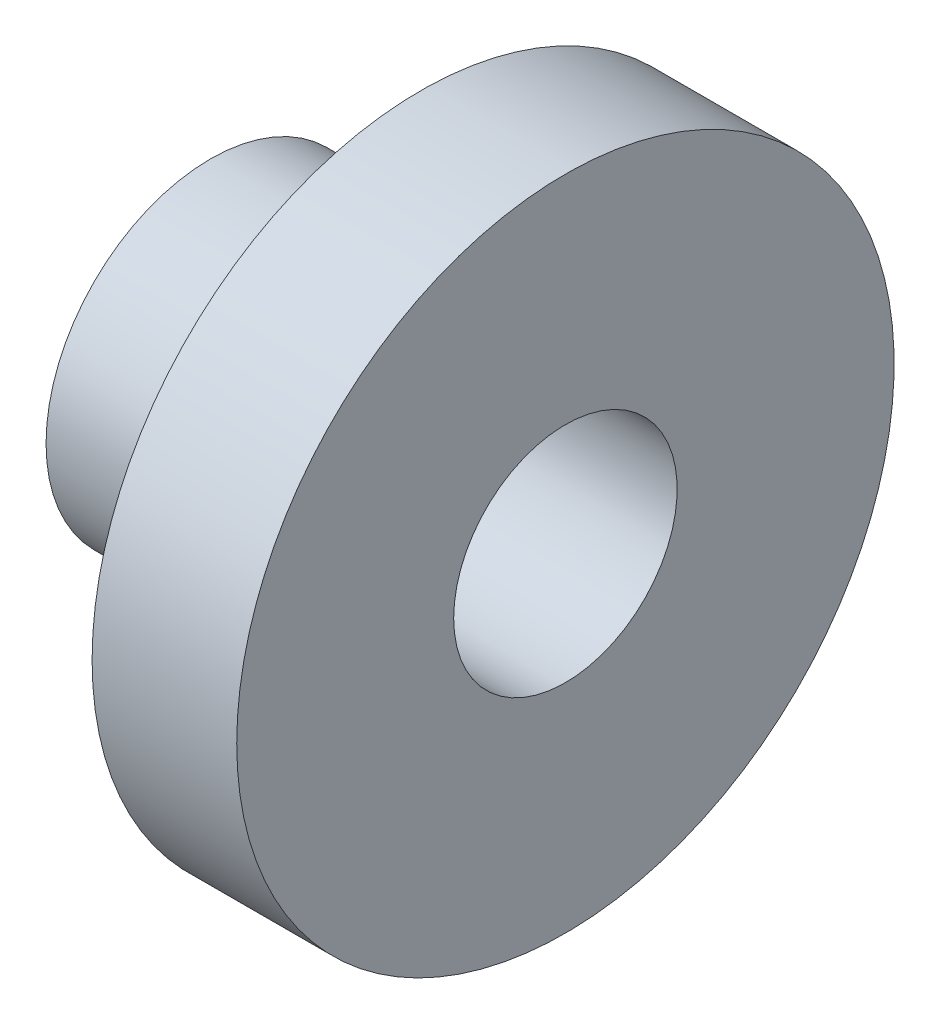
SolidWorks part; units mm, degrees
material "1.0037 (S235JR)"
ref_plane "Front Plane" through (0, 0, 0) normal (0, 0, 1) x (1, 0, 0)
ref_plane "Top Plane" through (0, 0, 0) normal (0, 1, 0) x (1, 0, 0)
ref_plane "Right Plane" through (0, 0, 0) normal (1, 0, 0) x (0, 0, -1)
sketch "Sketch3" plane through (0, 0, 0) normal (0, 0, 1) x (1, 0, 0)
  line L0 (-13.5, 0) -> (13.5, 0) construction
  line L1 (13.5, 0) -> (13.5, 25)
  line L2 (13.5, 25) -> (2.5, 25)
  line L3 (2.5, 25) -> (2.5, 12.5)
  line L4 (2.5, 12.5) -> (-13.5, 12.5)
  line L5 (-13.5, 12.5) -> (-13.5, 0)
  line L6 (-13.5, 8.5) -> (13.5, 8.5)
  dimension "D1" = 17
  dimension "D2" = 25
  dimension "D3" = 50
  dimension "D4" = 11
  dimension "D5" = 27
revolve "Revolve1" add sketch "Sketch3" angle 360 about L0
